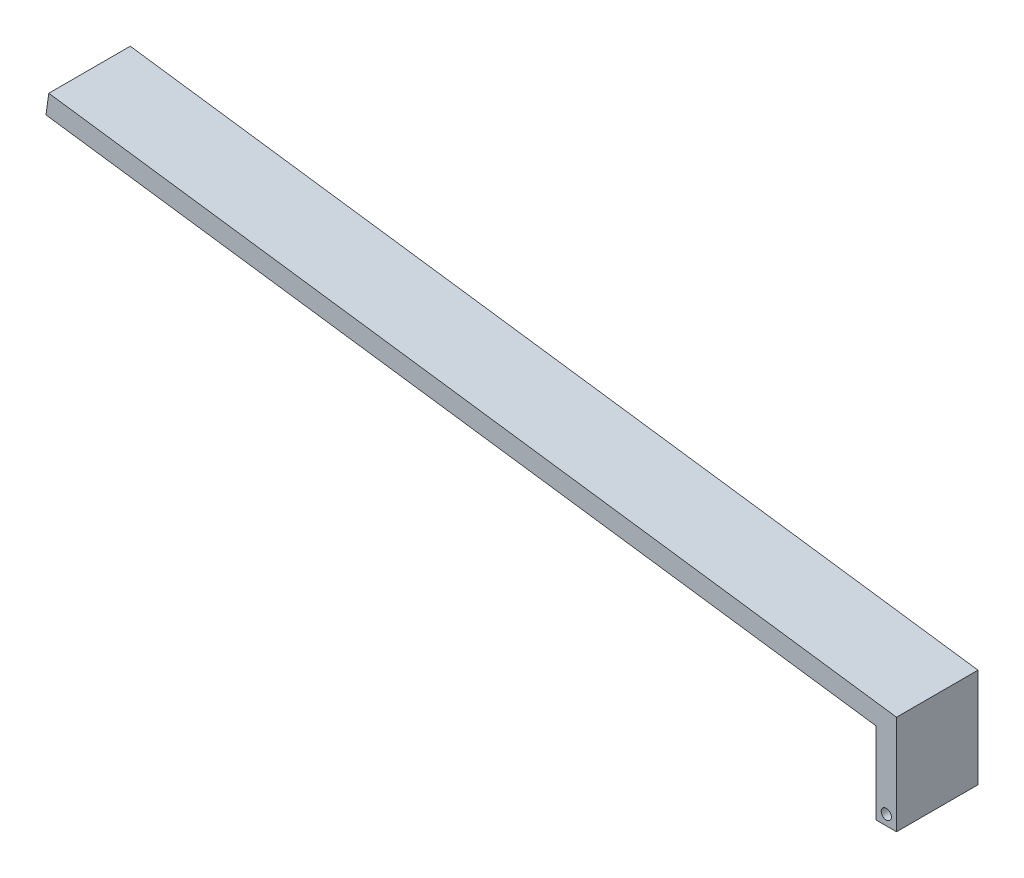
SolidWorks part; units mm, degrees
ref_plane "Front Plane" through (0, 0, 0) normal (0, 0, 1) x (1, 0, 0)
ref_plane "Top Plane" through (0, 0, 0) normal (0, 1, 0) x (1, 0, 0)
ref_plane "Right Plane" through (0, 0, 0) normal (1, 0, 0) x (0, 0, -1)
sketch "Sketch1" plane through (0, 0, 0) normal (0, 0, 1) x (1, 0, 0)
  line L0 (17.1044, -5.3208) -> (18.1044, -5.3208)
  line L1 (18.1044, -5.3208) -> (18.1044, -0.4488)
  line L2 (18.1044, -0.4488) -> (-23.5045, 5.2699)
  line L3 (-23.5045, 5.2699) -> (-23.6406, 4.2792)
  line L4 (-23.6406, 4.2792) -> (17.1044, -1.3208)
  line L5 (17.1044, -1.3208) -> (17.1044, -5.3208)
  dimension "D1" = 1
  dimension "D2" = 4
  dimension "D3" = 1
  dimension "D4" = 42
  dimension "D5" = 5.6
extrude "Extrude1" add sketch "Sketch1" along normal blind 4
sketch "Sketch2" plane through (0, 0, 4) normal (0, 0, 1) x (1, 0, 0)
  line L0 (17.1044, -5.3208) -> (18.1044, -5.3208) construction
  line L1 (18.1044, -5.3208) -> (18.1044, -0.4488) construction
  circle A0 centre (17.6044, -4.8208) radius 0.25
  dimension "D1" = 0.5
  dimension "D2" = 0.5
  dimension "D3" = 0.5
extrude "Extrude2" cut sketch "Sketch2" against normal blind 14
